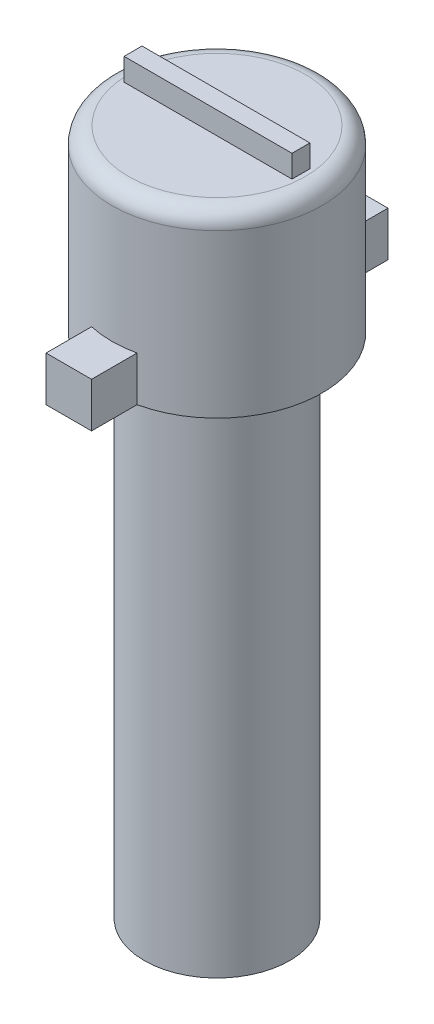
SolidWorks part; units mm, degrees
ref_plane "Front Plane" through (0, 0, 0) normal (0, 0, 1) x (1, 0, 0)
ref_plane "Top Plane" through (0, 0, 0) normal (0, 1, 0) x (1, 0, 0)
ref_plane "Right Plane" through (0, 0, 0) normal (1, 0, 0) x (0, 0, -1)
sketch "Sketch1" plane through (0, 0, 0) normal (0, 1, 0) x (1, 0, 0)
  circle A0 centre (0, 0) radius 3.25
  dimension "D1" = 6.5
extrude "Boss-Extrude1" add sketch "Sketch1" along normal blind 22.686 contours A0
sketch "Sketch2" plane through (0, 0, 0) normal (0, -1, 0) x (1, 0, 0)
  circle A1 centre (0, 0) radius 1.75
  dimension "D1" = 3.5
extrude "Cut-Extrude1" [suppressed] cut sketch "Sketch2" against normal blind 2.5
sketch "Sketch6" plane through (0, 22.686, 0) normal (0, 1, 0) x (1, 0, 0)
  circle A0 centre (0, 0) radius 4.7
  dimension "D1" = 9.4
extrude "Boss-Extrude2" add sketch "Sketch6" along normal blind 8 contours A0
sketch "Sketch7" plane through (0, 30.686, 0) normal (0, 1, 0) x (1, 0, 0)
  line L1 (-0.4, -3.75) -> (0.4, -3.75)
  line L2 (-0.4, -3.75) -> (-0.4, 3.75)
  line L3 (-0.4, 3.75) -> (0.4, 3.75)
  line L4 (0.4, -3.75) -> (0.4, 3.75)
  line L5 (-0.4, -3.75) -> (0.4, 3.75) construction
  line L6 (-0.4, 3.75) -> (0.4, -3.75) construction
  line L7 (-3.75, -0.4) -> (3.75, -0.4)
  line L8 (-3.75, -0.4) -> (-3.75, 0.4)
  line L9 (-3.75, 0.4) -> (3.75, 0.4)
  line L10 (3.75, -0.4) -> (3.75, 0.4)
  line L11 (-3.75, -0.4) -> (3.75, 0.4) construction
  line L12 (-3.75, 0.4) -> (3.75, -0.4) construction
  point P0 (0, 0)
  point P6 (0, 0)
  dimension "D1" = 0.8
  dimension "D2" = 7.5
  dimension "D3" = 7.5
  dimension "D4" = 0.8
sketch "Sketch8" plane through (0, 30.686, 0) normal (0, 1, 0) x (1, 0, 0)
  line L0 (0.4, 3.75) -> (-0.4, 3.75)
  line L1 (-0.4, 3.75) -> (-0.4, 0.4)
  line L2 (-0.4, -3.75) -> (-0.4, 3.75) construction
  line L3 (-3.75, 0.4) -> (3.75, 0.4) construction
  line L4 (-0.4, 0.4) -> (-3.75, 0.4)
  line L5 (-3.75, 0.4) -> (-3.75, -0.4)
  line L6 (-3.75, -0.4) -> (-0.4, -0.4)
  line L7 (-3.75, -0.4) -> (3.75, -0.4) construction
  line L8 (-0.4, -0.4) -> (-0.4, -3.75)
  line L9 (-0.4, -3.75) -> (0.4, -3.75)
  line L10 (0.4, -3.75) -> (0.4, -0.4)
  line L11 (0.4, -3.75) -> (0.4, 3.75) construction
  line L12 (0.4, -0.4) -> (3.75, -0.4)
  line L13 (3.75, -0.4) -> (3.75, 0.4)
  line L14 (3.75, 0.4) -> (0.4, 0.4)
  line L15 (0.4, 0.4) -> (0.4, 3.75)
extrude "Boss-Extrude3" add sketch "Sketch8" along normal blind 1
fillet "Fillet1" radius 0.75 1 edges at (0, 30.686, 4.7)
sketch "Sketch9" plane through (0, 30.686, 0) normal (0, 1, 0) x (1, 0, 0)
  line L1 (-0.4, 3.75) -> (0.4, 3.75)
  line L2 (-0.4, 3.75) -> (-0.4, 0.4)
  line L3 (-0.4, 0.4) -> (0.4, 0.4)
  line L4 (0.4, 3.75) -> (0.4, 0.4)
  line L5 (-0.4, -0.4) -> (0.4, -0.4)
  line L6 (-0.4, -0.4) -> (-0.4, -3.75)
  line L7 (-0.4, -3.75) -> (0.4, -3.75)
  line L8 (0.4, -0.4) -> (0.4, -3.75)
extrude "Cut-Extrude3" cut sketch "Sketch9" along normal up to surface (1 mm away) up to face at (0, 31.686, 0)
sketch "Sketch10" plane through (0, 22.686, 0) normal (0, -1, 0) x (1, 0, 0)
  line L0 (0, 4.7) -> (0, -4.7) construction
  line L1 (-1.016, 4.5889) -> (-1.016, 6.6209)
  line L2 (-1.016, 6.6209) -> (1.016, 6.6209)
  line L3 (1.016, 6.6209) -> (1.016, 4.5889)
  line L4 (-4.7, 0) -> (4.7, 0) construction
  line L5 (1.016, -6.6209) -> (1.016, -4.5889)
  line L6 (-1.016, -6.6209) -> (1.016, -6.6209)
  line L7 (-1.016, -4.5889) -> (-1.016, -6.6209)
  circle A0 centre (0, 0) radius 4.7 construction
  circle A2 centre (0, 0) radius 4.7
  circle A3 centre (0, 0) radius 4.7
  circle M5 centre (0, 0) radius 4.7
  dimension "D1" = 0
  dimension "D2" = 2.032
  dimension "D3" = 2.032
extrude "Boss-Extrude4" add sketch "Sketch10" against normal blind 2 contours L3 L2 L1 A3 M5 | L7 L6 L5 M5
